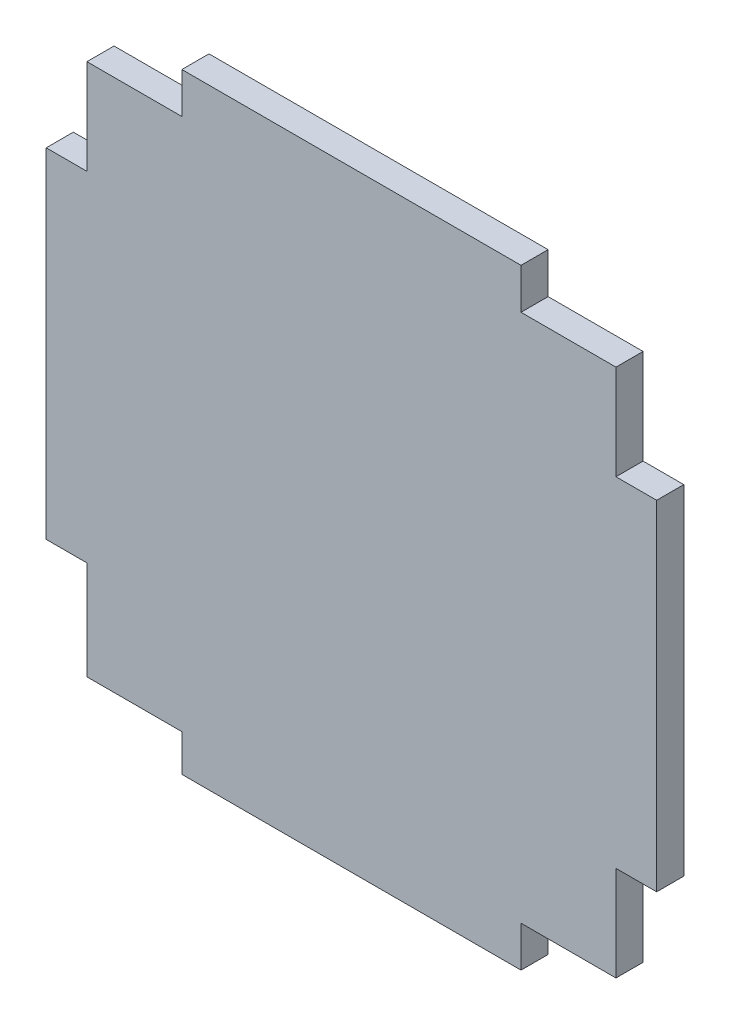
SolidWorks part; units mm, degrees
ref_plane "Front Plane" through (0, 0, 0) normal (0, 0, 1) x (1, 0, 0)
ref_plane "Top Plane" through (0, 0, 0) normal (0, 1, 0) x (1, 0, 0)
ref_plane "Right Plane" through (0, 0, 0) normal (1, 0, 0) x (0, 0, -1)
sketch "Sketch1" plane through (0, 0, 0) normal (0, 0, 1) x (1, 0, 0)
  line L1 (-22.5, -22.5) -> (22.5, -22.5)
  line L2 (-22.5, -22.5) -> (-22.5, 22.5)
  line L3 (-22.5, 22.5) -> (22.5, 22.5)
  line L4 (22.5, -22.5) -> (22.5, 22.5)
  line L5 (0, 22.5) -> (0, -22.5) construction
  line L6 (-22.5, 0) -> (22.5, 0) construction
  point P0 (0, 0)
  dimension "D1" = 45
  dimension "D2" = 45
extrude "Boss-Extrude1" add sketch "Sketch1" along normal blind 2
sketch "Sketch2" plane through (0, 0, 2) normal (0, 0, 1) x (1, 0, 0)
  line L1 (-22.5, -22.5) -> (-19.5, -22.5)
  line L2 (-22.5, -22.5) -> (-22.5, -12.5)
  line L3 (-22.5, -12.5) -> (-19.5, -12.5)
  line L4 (-19.5, -22.5) -> (-19.5, -12.5)
  line L5 (22.5, -22.5) -> (19.5, -22.5)
  line L6 (22.5, -22.5) -> (22.5, -12.5)
  line L7 (22.5, -12.5) -> (19.5, -12.5)
  line L8 (19.5, -22.5) -> (19.5, -12.5)
  line L9 (-22.5, 22.5) -> (-12.5, 22.5)
  line L10 (-22.5, 22.5) -> (-22.5, 19.5)
  line L11 (-22.5, 19.5) -> (-12.5, 19.5)
  line L12 (-12.5, 22.5) -> (-12.5, 19.5)
  line L13 (22.5, 22.5) -> (19.5, 22.5)
  line L14 (22.5, 22.5) -> (22.5, 12.5)
  line L15 (22.5, 12.5) -> (19.5, 12.5)
  line L16 (19.5, 22.5) -> (19.5, 12.5)
  line L17 (-22.5, 19.5) -> (-19.5, 19.5)
  line L18 (-22.5, 19.5) -> (-22.5, 12.5)
  line L19 (-22.5, 12.5) -> (-19.5, 12.5)
  line L20 (-19.5, 19.5) -> (-19.5, 12.5)
  line L21 (-19.5, -22.5) -> (-12.5, -22.5)
  line L22 (-19.5, -22.5) -> (-19.5, -19.7735)
  line L23 (-19.5, -19.7735) -> (-12.5, -19.7735)
  line L24 (-12.5, -22.5) -> (-12.5, -19.7735)
  line L25 (19.5, 22.5) -> (12.5, 22.5)
  line L26 (19.5, 22.5) -> (19.5, 19.5)
  line L27 (19.5, 19.5) -> (12.5, 19.5)
  line L28 (12.5, 22.5) -> (12.5, 19.5)
  line L29 (19.5, -22.5) -> (12.5, -22.5)
  line L30 (19.5, -22.5) -> (19.5, -19.5)
  line L31 (19.5, -19.5) -> (12.5, -19.5)
  line L32 (12.5, -22.5) -> (12.5, -19.5)
  line M16 (22.5, -22.5) -> (22.5, 22.5)
  line M17 (22.5, 22.5) -> (-22.5, 22.5)
  line M18 (-22.5, 22.5) -> (-22.5, -22.5)
  line M19 (-22.5, -22.5) -> (22.5, -22.5)
  dimension "D1" = 3
  dimension "D2" = 10
  dimension "D3" = 7
  dimension "D4" = 3
  dimension "D5" = 3
  dimension "D6" = 10
  dimension "D7" = 7
  dimension "D8" = 10
  dimension "D9" = 3
  dimension "D10" = 3
  dimension "D11" = 7
  dimension "D12" = 3
  dimension "D13" = 10
  dimension "D14" = 3
  dimension "D15" = 7
extrude "Cut-Extrude1" cut sketch "Sketch2" against normal blind 10 contours L20 L11 L19 M18 | L12 L11 M17 M18 | L28 L27 L16 M17 | L16 L15 M17 M16 | L32 L8 L31 M19 | L24 L23 L4 M19 | L4 L3 M19 M18
